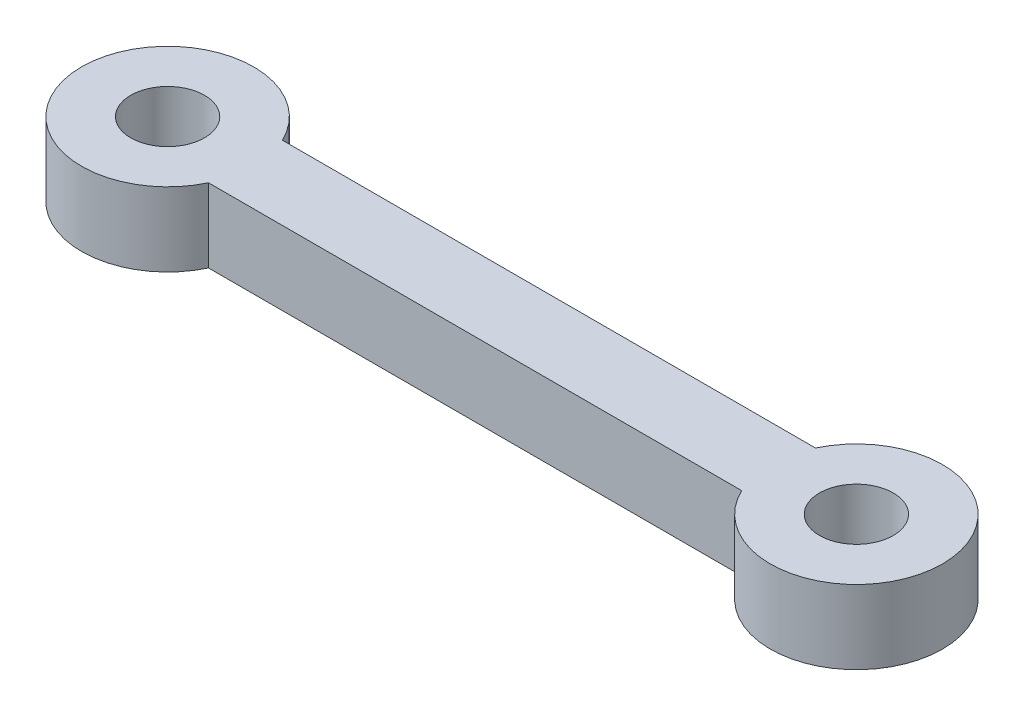
SolidWorks part; units mm, degrees
ref_plane "Front Plane" through (0, 0, 0) normal (0, 0, 1) x (1, 0, 0)
ref_plane "Top Plane" through (0, 0, 0) normal (0, 1, 0) x (1, 0, 0)
ref_plane "Right Plane" through (0, 0, 0) normal (1, 0, 0) x (0, 0, -1)
sketch "Sketch1" plane through (0, 0, 0) normal (0, 1, 0) x (1, 0, 0)
  line L4 (3.1623, 1.5) -> (24.8377, 1.5)
  line L8 (3.1623, -1.5) -> (24.8377, -1.5)
  arc A0 (3.1623, 1.5) -> (3.1623, -1.5) centre (0, 0) ccw
  arc A1 (24.8377, -1.5) -> (24.8377, 1.5) centre (28, 0) ccw
  dimension "D1" = 7
  dimension "D2" = 7
extrude "Boss-Extrude1" add sketch "Sketch1" along normal blind 3
sketch "Sketch2" plane through (0, 3, 0) normal (0, 1, 0) x (1, 0, 0)
  circle A0 centre (0, 0) radius 1.5
  circle A1 centre (28, 0) radius 1.5
  dimension "D1" = 3
  dimension "D2" = 3
extrude "Cut-Extrude1" cut sketch "Sketch2" against normal blind 3
